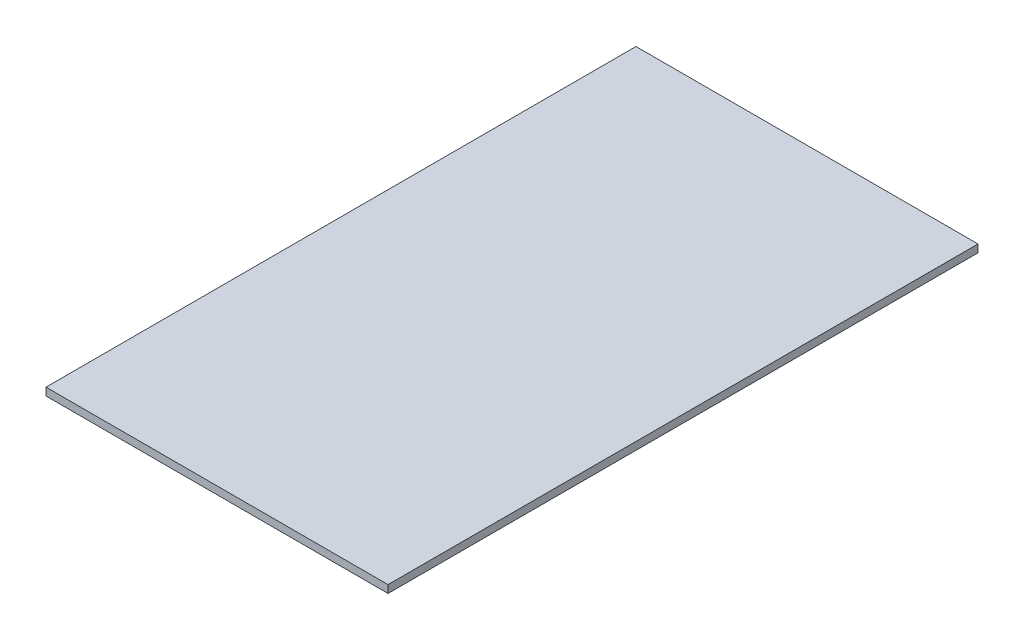
SolidWorks part; units mm, degrees
ref_plane "Front Plane" through (0, 0, 0) normal (0, 0, 1) x (1, 0, 0)
ref_plane "Top Plane" through (0, 0, 0) normal (0, 1, 0) x (1, 0, 0)
ref_plane "Right Plane" through (0, 0, 0) normal (1, 0, 0) x (0, 0, -1)
sketch "Sketch1" plane through (0, 0, 0) normal (0, 1, 0) x (1, 0, 0)
  line L1 (0, 0) -> (80, 0)
  line L2 (0, 0) -> (0, 138)
  line L3 (0, 138) -> (80, 138)
  line L4 (80, 0) -> (80, 138)
  dimension "D1" = 80
  dimension "D2" = 138
extrude "Boss-Extrude1" add sketch "Sketch1" along normal blind 1.8
